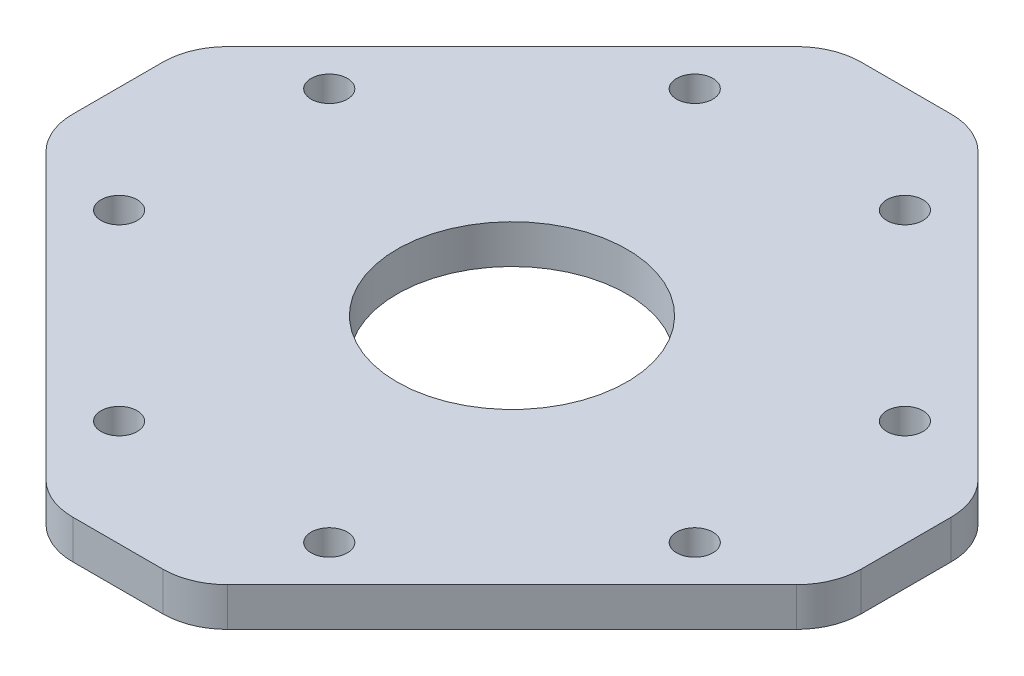
SolidWorks part; units mm, degrees
ref_plane "Front Plane" through (0, 0, 0) normal (0, 0, 1) x (1, 0, 0)
ref_plane "Top Plane" through (0, 0, 0) normal (0, 1, 0) x (1, 0, 0)
ref_plane "Right Plane" through (0, 0, 0) normal (1, 0, 0) x (0, 0, -1)
sketch "Sketch1" plane through (0, 0, 0) normal (0, 1, 0) x (1, 0, 0)
  line L0 (3.4914, 30.5) -> (-3.4914, 30.5)
  line L1 (-7.0269, 29.0355) -> (-29.0355, 7.0269)
  line L2 (-30.5, 3.4914) -> (-30.5, -3.4914)
  line L3 (-29.0355, -7.0269) -> (-7.0269, -29.0355)
  line L4 (-3.4914, -30.5) -> (3.4914, -30.5)
  line L5 (7.0269, -29.0355) -> (29.0355, -7.0269)
  line L6 (30.5, -3.4914) -> (30.5, 3.4914)
  line L7 (29.0355, 7.0269) -> (7.0269, 29.0355)
  arc A0 (7.0269, 29.0355) -> (3.4914, 30.5) centre (3.4914, 25.5) ccw
  arc A1 (-3.4914, 30.5) -> (-7.0269, 29.0355) centre (-3.4914, 25.5) ccw
  arc A2 (-29.0355, 7.0269) -> (-30.5, 3.4914) centre (-25.5, 3.4914) ccw
  arc A3 (-30.5, -3.4914) -> (-29.0355, -7.0269) centre (-25.5, -3.4914) ccw
  arc A4 (-7.0269, -29.0355) -> (-3.4914, -30.5) centre (-3.4914, -25.5) ccw
  arc A5 (3.4914, -30.5) -> (7.0269, -29.0355) centre (3.4914, -25.5) ccw
  arc A6 (29.0355, -7.0269) -> (30.5, -3.4914) centre (25.5, -3.4914) ccw
  arc A7 (30.5, 3.4914) -> (29.0355, 7.0269) centre (25.5, 3.4914) ccw
  circle A8 centre (0, 0) radius 8.9
  circle A9 centre (8.1317, -22.2739) radius 1.4
  circle A10 centre (-8.1317, -22.2739) radius 1.4
  circle A11 centre (-22.2739, -8.1317) radius 1.4
  circle A12 centre (22.2739, -8.1317) radius 1.4
  circle A13 centre (22.2739, 8.1317) radius 1.4
  circle A14 centre (8.1317, 22.2739) radius 1.4
  circle A15 centre (-8.1317, 22.2739) radius 1.4
  circle A16 centre (-22.2739, 8.1317) radius 1.4
  dimension "D2" = 17.8
  dimension "D3" = 2.8
  dimension "D1" = 51
extrude "Boss-Extrude1" add sketch "Sketch1" along normal blind 3
